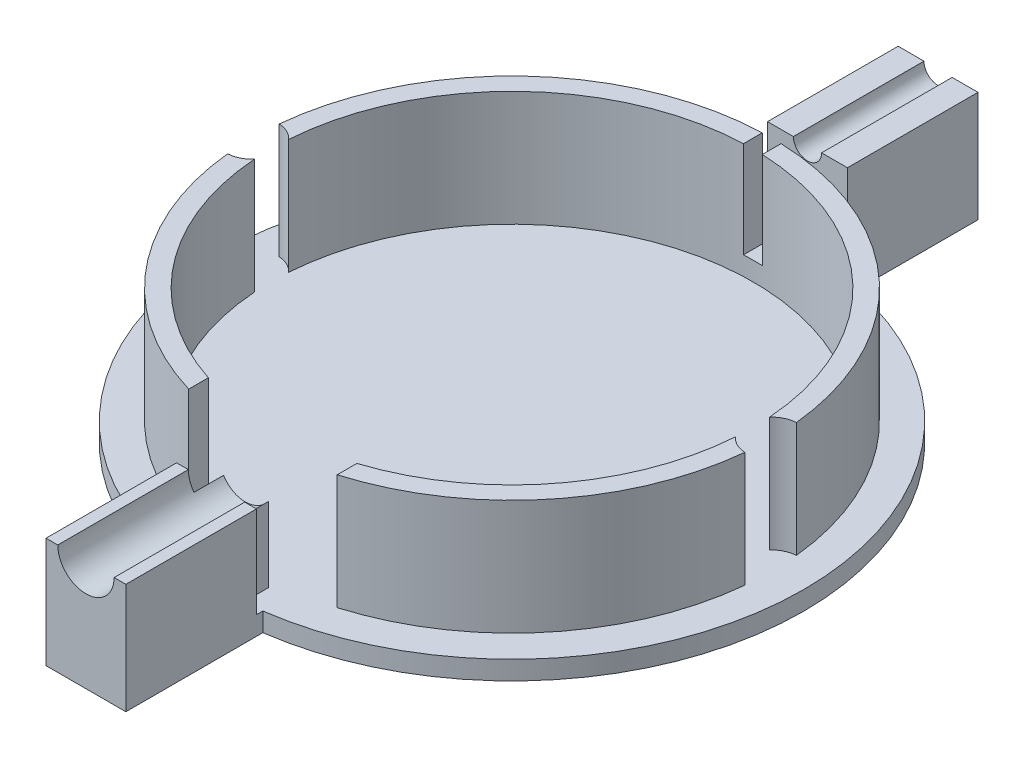
SolidWorks part; units mm, degrees
ref_plane "Front Plane" through (0, 0, 0) normal (0, 0, 1) x (1, 0, 0)
ref_plane "Top Plane" through (0, 0, 0) normal (0, 1, 0) x (1, 0, 0)
ref_plane "Right Plane" through (0, 0, 0) normal (1, 0, 0) x (0, 0, -1)
sketch "Sketch1" plane through (0, 0, 0) normal (0, 1, 0) x (1, 0, 0)
  circle A0 centre (0, 0) radius 31.06
  dimension "D1" = 62.12
extrude "Boss-Extrude1" add sketch "Sketch1" along normal blind 2
sketch "Sketch2" plane through (0, 2, 0) normal (0, 1, 0) x (1, 0, 0)
  circle A0 centre (0, 0) radius 27.66
  circle A1 centre (0, 0) radius 25.66
  circle A2 centre (0, 0) radius 31.06 construction
  dimension "D1" = 2
  dimension "D2" = 3.4
extrude "Boss-Extrude2" add sketch "Sketch2" along normal blind 12.25
sketch "Sketch4" plane through (0, 14.25, 0) normal (0, 1, 0) x (1, 0, 0)
  arc A0 (25.5956, -1.8168) -> (27.5233, -2.7466) centre (27.66, 0) ccw
  circle A1 centre (0, 0) radius 27.66 construction
  arc A2 (-27.5233, -2.7466) -> (-25.5956, -1.8168) centre (-27.66, 0) ccw
  circle A3 centre (0, 0) radius 25.66 construction
  arc A4 (-25.5956, 1.8168) -> (-25.5956, -1.8168) centre (0, 0) ccw
  arc A5 (-27.5233, 2.7466) -> (-27.5233, -2.7466) centre (0, 0) ccw
  arc A6 (25.5956, -1.8168) -> (25.5956, 1.8168) centre (0, 0) ccw
  arc A7 (27.5233, -2.7466) -> (27.5233, 2.7466) centre (0, 0) ccw
  arc A8 (-25.5956, 1.8168) -> (-27.5233, 2.7466) centre (-27.66, 0) ccw
  arc A9 (27.5233, 2.7466) -> (25.5956, 1.8168) centre (27.66, 0) ccw
  circle M1 centre (0, 0) radius 27.66
  circle M2 centre (0, 0) radius 25.66
  dimension "D1" = 5.5
  dimension "D2" = 5.5
extrude "Cut-Extrude1" cut sketch "Sketch4" against normal up to surface (12.25 mm away) contours A9 A0 M1 M2 | A4 A2 A5 A8 up to face at (0, 2, 31.06)
sketch "Sketch5" plane through (0, 14.25, 0) normal (0, 1, 0) x (1, 0, 0)
  line L0 (0, -25.66) -> (0, -27.66)
  line L1 (3, -25.484) -> (3, -27.4968)
  line L2 (-3, -25.484) -> (-3, -27.4968)
  line L3 (3, -25.66) -> (3, -27.66) construction
  line L4 (-3, -25.66) -> (-3, -27.66) construction
  arc A0 (-25.5956, -1.8168) -> (25.5956, -1.8168) centre (0, 0) ccw construction
  arc A1 (-27.5233, -2.7466) -> (27.5233, -2.7466) centre (0, 0) ccw construction
  arc A3 (-3, -25.484) -> (3, -25.484) centre (0, 0) ccw
  arc A4 (-3, -27.4968) -> (3, -27.4968) centre (0, 0) ccw
  arc M2 (-27.5233, -2.7466) -> (27.5233, -2.7466) centre (0, 0) ccw
  arc M4 (25.5956, -1.8168) -> (-25.5956, -1.8168) centre (0, 0) cw
  dimension "D1" = 3
  dimension "D2" = 3
extrude "Cut-Extrude2" cut sketch "Sketch5" against normal blind 6.8 contours L2 L0 M4 M2 | L1 L0 M4 M2
sketch "Sketch7" plane through (0, 2, 0) normal (0, 1, 0) x (1, 0, 0)
  line L2 (2.4, -28.3014) -> (2.4, -30.9671)
  line L3 (-2.4, -28.3014) -> (-2.4, -30.9671)
  line L4 (3, -25.484) -> (3, -27.4968) construction
  circle A0 centre (0, 0) radius 31.06 construction
  arc A1 (-2.4, -30.9671) -> (2.4, -30.9671) centre (0, 0) ccw
  arc A4 (-2.4, -28.3014) -> (2.4, -28.3014) centre (0, 0.0572) ccw
  dimension "D1" = 4.8
  dimension "D2" = 0.6
extrude "Boss-Extrude5" add sketch "Sketch7" along normal up to surface (12.25 mm away) up to face at (-16.9184, 14.25, 16.5387)
ref_plane "Plane1" through (0, 0, 31.06) normal (0, 0, 1) x (1, 0, 0)
sketch "Sketch8" plane through (0, 0, 31.06) normal (0, 0, 1) x (1, 0, 0)
  line L0 (2.4, 14.25) -> (-2.4, 14.25) construction
  line L1 (2.4, 14.25) -> (-2.4, 14.25)
  line L2 (31.06, 2) -> (-31.06, 2) construction
  line L3 (2.4, 2) -> (-2.4, 2)
  line L4 (2.4, 14.25) -> (2.4, 2) construction
  line L5 (2.4, 14.25) -> (2.4, 2)
  line L6 (-2.4, 14.25) -> (-2.4, 2) construction
  line L7 (-2.4, 14.25) -> (-2.4, 2)
  line L8 (-2.4, 11.75) -> (2.4, 11.75)
  circle A0 centre (0, 11.75) radius 3
  dimension "D2" = 6
  dimension "D1" = 9.75
extrude "Cut-Extrude3" cut sketch "Sketch8" against normal blind 7.6 contours L5 A0 L1 L7 L8 | L5 A0 | L7 A0 L5 L8 | L7 A0 | A0 L5 L1 | A0 L1 L7
sketch "Sketch9" plane through (0, 0, 0) normal (0, 0, 1) x (1, 0, 0)
  line L0 (25.5956, 14.25) -> (-25.5956, 14.25) construction
  line L1 (-1, 4) -> (1, 4)
  line L2 (-1, 4) -> (-1, 14.25)
  line L3 (-1, 6) -> (1, 6)
  line L4 (1, 4) -> (1, 14.25)
  line L5 (-1, 4) -> (1, 6) construction
  line L6 (-1, 6) -> (1, 4) construction
  line L7 (1, 14.25) -> (-1, 14.25)
  point P0 (0, 5)
  dimension "D1" = 5
  dimension "D2" = 2
  dimension "D3" = 2
extrude "Cut-Extrude4" cut sketch "Sketch9" against normal through all contours L1 L4 L3 L2 | L4 L7 L2 L3
sketch "Sketch11" plane through (0, 14.25, 0) normal (0, 1, 0) x (1, 0, 0)
  line L2 (-7.9, -27.9874) -> (7.9, -27.9874)
  line L4 (7.9, -24.1658) -> (-7.9, -24.1658)
  line L5 (7.9, -24.1658) -> (7.9, -28.7542)
  line L6 (7.9, -28.7542) -> (-7.9, -28.7542)
  line L7 (-7.9, -24.1658) -> (-7.9, -28.7542)
  line L8 (7.9, -24.1658) -> (-7.9, -28.7542) construction
  line L9 (7.9, -28.7542) -> (-7.9, -24.1658) construction
  arc A2 (3, -25.484) -> (25.5956, -1.8168) centre (0, 0) ccw construction
  arc A3 (3, -25.484) -> (25.5956, -1.8168) centre (0, 0) ccw
  point P7 (0, -26.46)
  dimension "D1" = 15.8
extrude "Cut-Extrude5" cut sketch "Sketch11" against normal up to surface (12.25 mm away)
sketch "Sketch12" plane through (0, 0, 0) normal (0, -1, 0) x (1, 0, 0)
  line L0 (0, 31.06) -> (0, 45.35)
  line L1 (-4.25, 31.06) -> (4.25, 31.06)
  line L2 (4.25, 30.7679) -> (4.25, 45.35)
  line L3 (-4.25, 30.7679) -> (-4.25, 45.35)
  line L4 (-4.25, 45.35) -> (4.25, 45.35)
  line L5 (5.5481, 0) -> (-4.25, 0)
  line L6 (-14.4841, 45.35) -> (8.5, 45.35) construction
  line L7 (-14.4841, 31.06) -> (8.5, 31.06) construction
  line L8 (-4.25, -45.35) -> (4.25, -45.35)
  line L9 (-4.25, -30.7679) -> (-4.25, -45.35)
  line L10 (4.25, -30.7679) -> (4.25, -45.35)
  line L11 (-4.25, -31.06) -> (4.25, -31.06)
  line L12 (0, -31.06) -> (0, -45.35)
  circle A0 centre (0, 0) radius 31.06 construction
  circle A1 centre (0, 0) radius 31.06
  point P6 (4.25, 0)
  point P8 (-4.25, 0)
  circle M1 centre (0, 0) radius 31.06
  dimension "D1" = 14.29
  dimension "D5" = 14.29
extrude "Boss-Extrude7" add sketch "Sketch12" against normal blind 2 contours L4 L0 L1 L2 | L4 L3 L1 L0 | L2 L1 M1 | L3 L1 M1 | L11 L12 L8 L10 | L12 L11 L9 L8 | L9 L11 M1 | L11 L10 M1 | A1
sketch "Sketch13" plane through (0, 0, 45.35) normal (0, 0, 1) x (1, 0, 0)
  line L0 (-4.25, 2) -> (4.25, 2) construction
  line L1 (-4.25, 2) -> (4.25, 2)
  line L2 (-3, 11.75) -> (-4.25, 11.75)
  line L3 (4.25, 2) -> (-4.25, 2)
  line L4 (4.25, 2) -> (4.25, 11.75)
  line L5 (4.25, 11.75) -> (3, 11.75)
  line L6 (-4.25, 2) -> (-4.25, 11.75)
  arc A0 (-3, 11.75) -> (3, 11.75) centre (0, 11.75) ccw
  dimension "D2" = 6
  dimension "D1" = 9.75
extrude "Boss-Extrude8" add sketch "Sketch13" against normal blind 13.9 contours L3 L6 L2 A0 L5 L4
sketch "Sketch14" plane through (0, 0, 31.06) normal (0, 0, 1) x (1, 0, 0)
  line L3 (-2.4, 2) -> (2.4, 2)
  line L4 (2.4, 2) -> (2.4, 9.95)
  line L5 (-2.4, 9.95) -> (-2.4, 2)
  line L6 (-2.4, 2) -> (2.4, 2)
  line L7 (2.4, 2) -> (2.4, 9.95)
  line L8 (-2.4, 9.95) -> (-2.4, 2)
  arc A1 (-2.4, 9.95) -> (2.4, 9.95) centre (0, 11.75) ccw
  arc A2 (-2.4, 9.95) -> (2.4, 9.95) centre (0, 11.75) ccw
  dimension "D1" = 0
extrude "Boss-Extrude9" add sketch "Sketch14" along normal blind 2 and the other way blind 2
sketch "Sketch15" plane through (0, 0, -45.35) normal (0, 0, -1) x (-1, 0, 0)
  line L0 (-1.5, 11.75) -> (-4.25, 11.75)
  line L1 (4.25, 0) -> (-4.25, 0)
  line L2 (4.25, 0) -> (4.25, 11.75)
  line L3 (4.25, 11.75) -> (1.5, 11.75)
  line L4 (-4.25, 0) -> (-4.25, 11.75)
  arc A0 (-1.5, 11.75) -> (1.5, 11.75) centre (0, 11.75) ccw
  dimension "D2" = 3
  dimension "D1" = 11.75
extrude "Boss-Extrude10" add sketch "Sketch15" against normal blind 13.9
